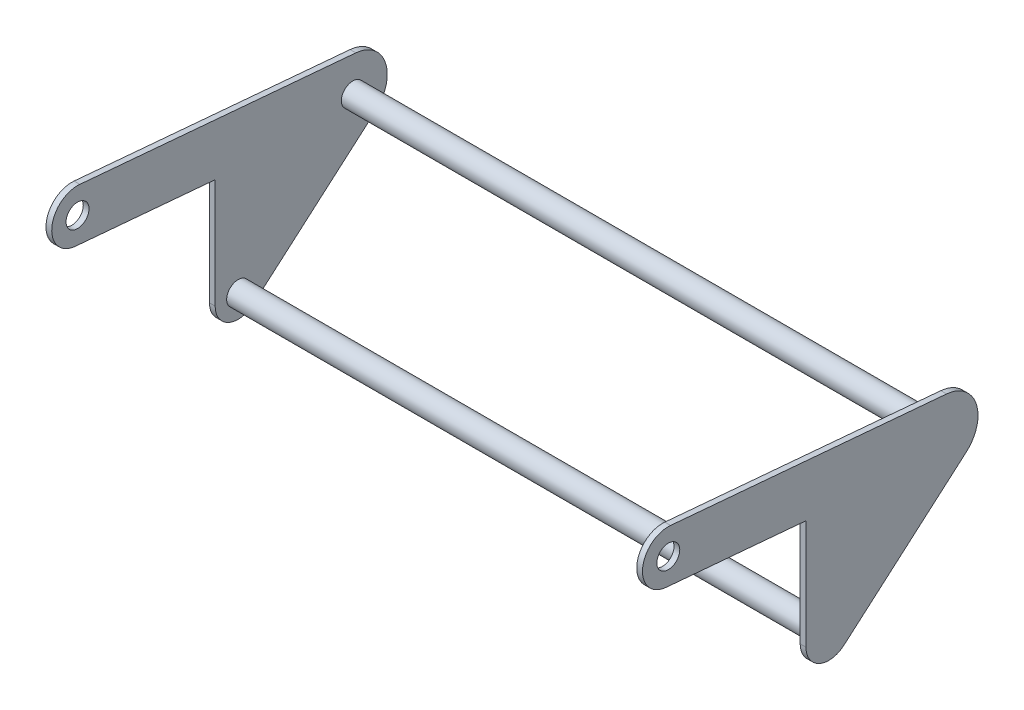
SolidWorks part; units mm, degrees
ref_plane "Front Plane" through (0, 0, 0) normal (0, 0, 1) x (1, 0, 0)
ref_plane "Top Plane" through (0, 0, 0) normal (0, 1, 0) x (1, 0, 0)
ref_plane "Right Plane" through (0, 0, 0) normal (1, 0, 0) x (0, 0, -1)
sketch "Sketch1" plane through (0, 0, 0) normal (1, 0, 0) x (0, 0, -1)
  line L0 (-180.2905, 134.7617) -> (-25.4, 121.2105)
  line L1 (-25.4, 121.2105) -> (-25.4, 0)
  line L2 (16.6456, -19.1856) -> (151.9683, 98.2217)
  line L3 (130.3206, 164.955) -> (-175.3095, 191.6942)
  line L4 (0, -25.4) -> (318.1018, -25.4) construction
  circle A0 centre (318.1018, 50.8) radius 76.2 construction
  arc A1 (-25.4, 0) -> (16.6456, -19.1856) centre (0, 0) ccw
  arc A2 (151.9683, 98.2217) -> (130.3206, 164.955) centre (127, 127) ccw
  arc A3 (-175.3095, 191.6942) -> (-180.2905, 134.7617) centre (-177.8, 163.2279) ccw
  circle A4 centre (0, 0) radius 12.7 construction
  circle A5 centre (127, 127) radius 12.7 construction
  point P13 (-186.7308, -121.9427)
  point P14 (-292.1, 114.189)
  point P16 (318.1018, 50.8)
  point P17 (127.7913, 114.3)
  point P18 (-170.5563, -95.4402)
  dimension "D1" = 152.4
  dimension "D2" = 127
  dimension "D4" = 25.4
  dimension "D5" = 25.4
  dimension "D6" = 57.15
  dimension "D9" = 38.1
  dimension "D3" = 152.4
  dimension "D7" = 152.4
  dimension "D8" = 95
extrude "Boss-Extrude1" add sketch "Sketch1" along normal blind 660.4
sketch "Sketch2" plane through (0, 0, 0) normal (0, 1, 0) x (1, 0, 0)
  line L0 (0, 130.3206) -> (0, -175.3095) construction
  line L1 (6.35, 165.1) -> (654.05, 165.1)
  line L2 (6.35, 165.1) -> (6.35, -206.375)
  line L3 (6.35, -206.375) -> (654.05, -206.375)
  line L4 (654.05, 165.1) -> (654.05, -206.375)
  line L5 (6.35, 165.1) -> (654.05, -206.375) construction
  line L6 (6.35, -206.375) -> (654.05, 165.1) construction
  line L7 (660.4, 130.3206) -> (660.4, -175.3095) construction
  line L8 (660.4, 165.1) -> (0, 165.1) construction
  line L9 (0, -206.375) -> (660.4, -206.375) construction
  point P0 (330.2, -20.6375)
  dimension "D1" = 6.35
  dimension "D2" = 6.35
extrude "Cut-Extrude1" cut sketch "Sketch2" against normal through all both and the other way through all
sketch "Sketch3" plane through (660.4, 0, 0) normal (1, 0, 0) x (0, 0, -1)
  circle A0 centre (127, 127) radius 12.7
  circle A1 centre (0, 0) radius 12.7
  circle A3 centre (127, 127) radius 12.7 construction
extrude "Boss-Extrude2" add sketch "Sketch3" against normal up to body
sketch "Sketch4" plane through (660.4, 0, 0) normal (1, 0, 0) x (0, 0, -1)
  circle A0 centre (-177.8, 163.2279) radius 12.7
  dimension "D1" = 25.4
extrude "Cut-Extrude2" cut sketch "Sketch4" against normal through all both and the other way through all
